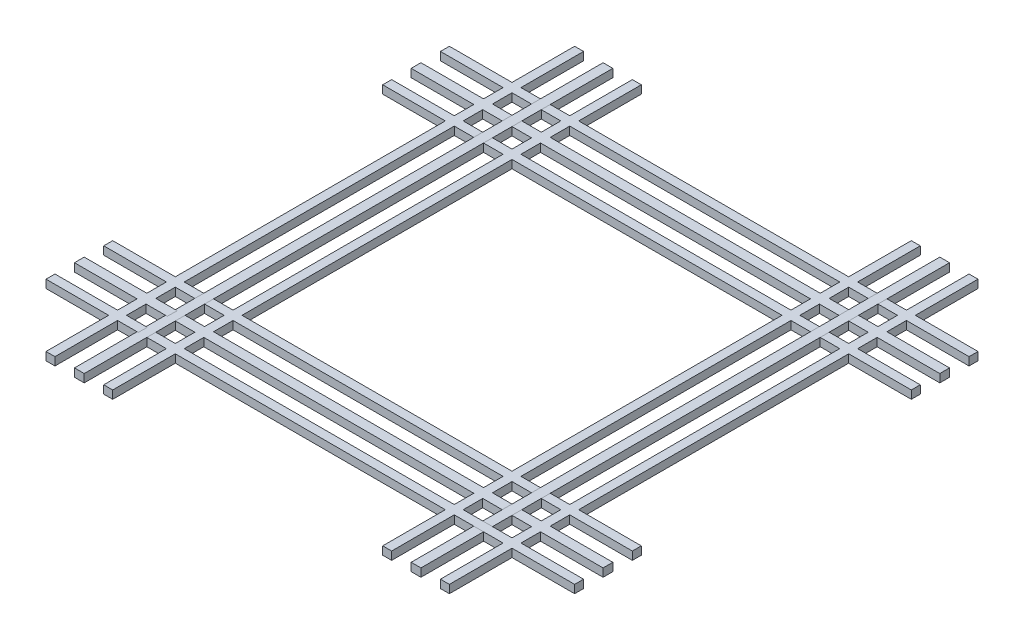
SolidWorks part; units mm, degrees
material "松木"
ref_plane "前视基准面" through (0, 0, 0) normal (0, 0, 1) x (1, 0, 0)
ref_plane "上视基准面" through (0, 0, 0) normal (0, 1, 0) x (1, 0, 0)
ref_plane "右视基准面" through (0, 0, 0) normal (1, 0, 0) x (0, 0, -1)
sketch "草图1" plane through (0, 0, 0) normal (0, 1, 0) x (1, 0, 0)
  line L1 (0, 0) -> (120, 0)
  line L2 (0, 0) -> (0, 6500)
  line L3 (0, 6500) -> (120, 6500)
  line L4 (120, 0) -> (120, 6500)
  dimension "D1" = 6500
  dimension "D2" = 120
extrude "凸台-拉伸1" add sketch "草图1" along normal blind 100
pattern_linear "阵列(线性)1" count 2 spacing 4140 along (1, 0, 0) of "凸台-拉伸1"
ref_plane "基准面4" through (2130, 0, 0) normal (1, 0, 0) x (0, 0, -1)
sketch "草图2" plane through (0, 0, 0) normal (0, 1, 0) x (1, 0, 0)
  line L0 (4260, 3250) -> (0, 3250)
  line L1 (4260, 0) -> (4260, 6500) construction
  line L2 (0, 6500) -> (0, 0) construction
  line L3 (2130, 3250) -> (2130, 3550)
  dimension "D1" = 300
sketch "草图3" plane through (2130, 0, 0) normal (1, 0, 0) x (0, 0, -1)
  line L0 (3250, 0) -> (3250, 200)
  dimension "D1" = 200
pattern_circular "阵列(圆周)1" count 2 every 90 about axis through (2130, 0, -3250) along (0, 1, 0) of bodies 101 102
sketch "草图4" plane through (0, 100, 0) normal (0, 1, 0) x (1, 0, 0)
  line L0 (120, 0) -> (120, 6500) construction
  line L1 (360, 6500) -> (470, 6500)
  line L2 (360, 6500) -> (360, 0)
  line L3 (360, 0) -> (470, 0)
  line L4 (470, 6500) -> (470, 0)
  line L5 (120, 6500) -> (0, 6500) construction
  dimension "D1" = 110
  dimension "D2" = 240
extrude "凸台-拉伸2" add sketch "草图4" against normal blind 100
pattern_circular "阵列(圆周)3" count 4 over 360 about axis through (2130, 0, -3250) along (0, 1, 0) of "凸台-拉伸2"
sketch "草图5" plane through (0, 100, 0) normal (0, 1, 0) x (1, 0, 0)
  line L0 (120, 6500) -> (0, 6500) construction
  line L1 (-240, 0) -> (-350, 0)
  line L2 (-240, 0) -> (-240, 6500)
  line L3 (-240, 6500) -> (-350, 6500)
  line L4 (-350, 0) -> (-350, 6500)
  line L5 (0, 6500) -> (0, 0) construction
  dimension "D1" = 110
  dimension "D2" = 240
extrude "凸台-拉伸3" add sketch "草图5" against normal blind 100
pattern_circular "阵列(圆周)4" count 4 over 360 about axis through (2130, 0, -3250) along (0, 1, 0) of "凸台-拉伸3"
